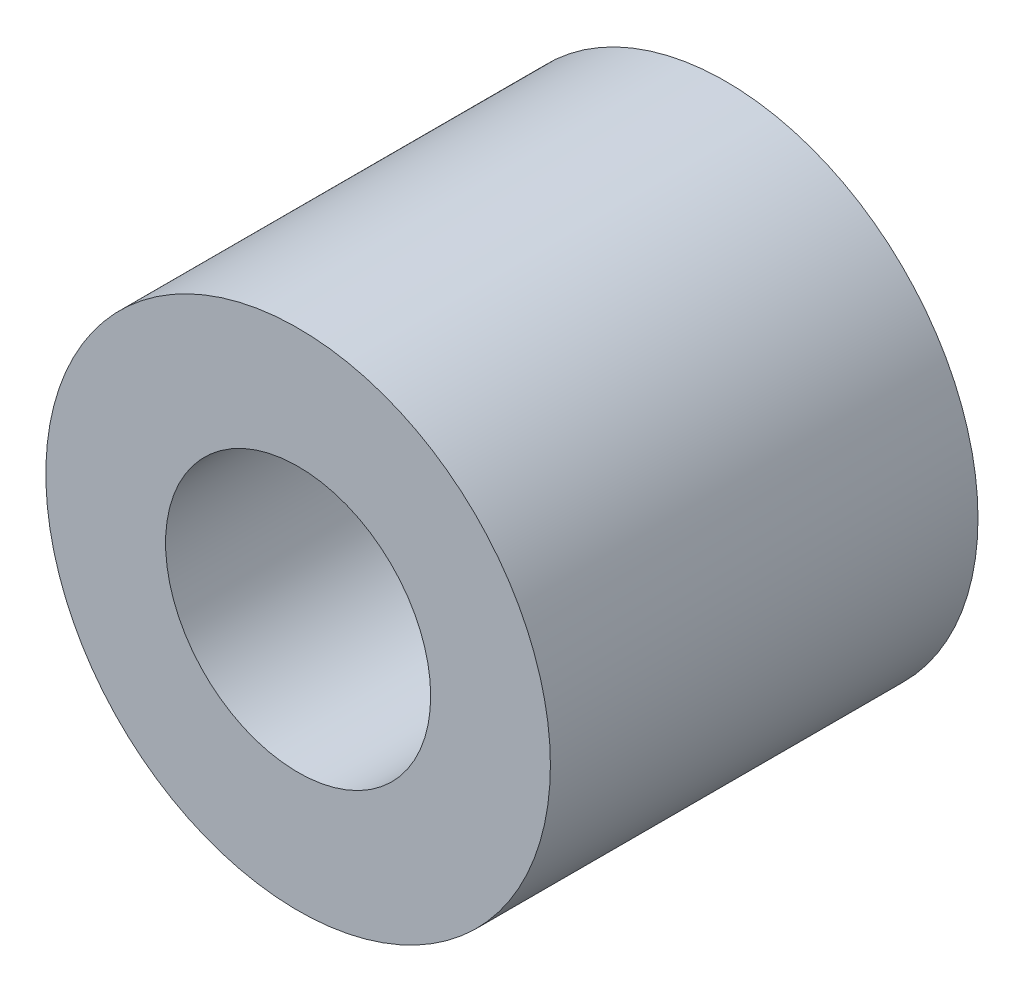
SolidWorks part; units mm, degrees
ref_plane "Front" through (0, 0, 0) normal (0, 0, 1) x (1, 0, 0)
ref_plane "Top" through (0, 0, 0) normal (0, 1, 0) x (1, 0, 0)
ref_plane "Right" through (0, 0, 0) normal (1, 0, 0) x (0, 0, -1)
sketch "Sketch1" plane through (0, 0, 0) normal (0, 0, 1) x (1, 0, 0)
  circle A0 centre (0, 0) radius 2.95
  dimension "D1" = 5.9
extrude "Boss-Extrude1" add sketch "Sketch1" along normal blind 5
sketch "Sketch4" plane through (0, 0, 5) normal (0, 0, 1) x (1, 0, 0)
  circle A0 centre (0, 0) radius 1.55
  dimension "D1" = 3.1
extrude "Cut-Extrude1" cut sketch "Sketch4" against normal through all
